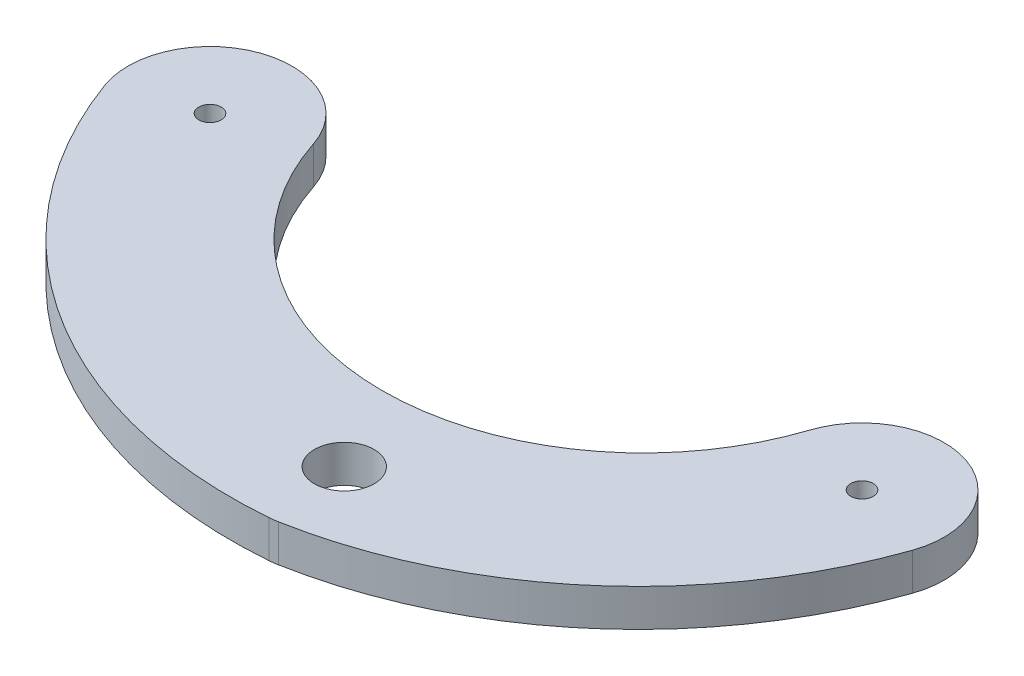
SolidWorks part; units mm, degrees
ref_plane "Front Plane" through (0, 0, 0) normal (0, 0, 1) x (1, 0, 0)
ref_plane "Top Plane" through (0, 0, 0) normal (0, 1, 0) x (1, 0, 0)
ref_plane "Right Plane" through (0, 0, 0) normal (1, 0, 0) x (0, 0, -1)
sketch "Sketch2" plane through (0, 0, 0) normal (0, 1, 0) x (1, 0, 0)
  line L1 (87.4, 0) -> (87.4, -1.5) construction
  line L2 (85.9, 0) -> (87.4, 0) construction
  circle A0 centre (0, 0) radius 1.5
  arc A1 (10.45, 3.4347) -> (-10.3302, -3.7799) centre (0, 0) ccw
  circle A2 centre (87.4, 0) radius 1.5
  arc A3 (97.7818, -3.6356) -> (76.95, 3.4347) centre (87.4, 0) ccw
  circle A4 centre (50, -32) radius 4
  arc A5 (50.8943, -42.9636) -> (51.9859, -42.8192) centre (50, -32) ccw
  arc A6 (10.45, 3.4347) -> (76.95, 3.4347) centre (43.7, 14.3635) ccw
  arc A7 (-10.3302, -3.7799) -> (51.4434, -42.9163) centre (46.0162, 16.8378) ccw
  arc A8 (51.4434, -42.9163) -> (97.7818, -3.6356) centre (41.1536, 16.1948) ccw
  point P3 (0, 0)
  point P8 (0, 0)
  point P13 (60.2761, 9.3662)
  point P20 (13.9436, 18.7907)
  point P22 (-157.5408, 61.8458)
  point P23 (0, 0)
  point P26 (27.6089, 16.7371)
  dimension "D2" = 22
  dimension "D4" = 3
  dimension "D5" = 22
  dimension "D8" = 8
  dimension "D9" = 22
  dimension "D10" = 70
  dimension "D11" = 120
  dimension "D12" = 120
  dimension "D13" = 44.2255
  dimension "D3" = 87.4
  dimension "D15" = 59.3633
extrude "Boss-Extrude1" add sketch "Sketch2" along normal blind 5 contours A5 A8 A3 A6 A1 A7 A0 A2 A4
